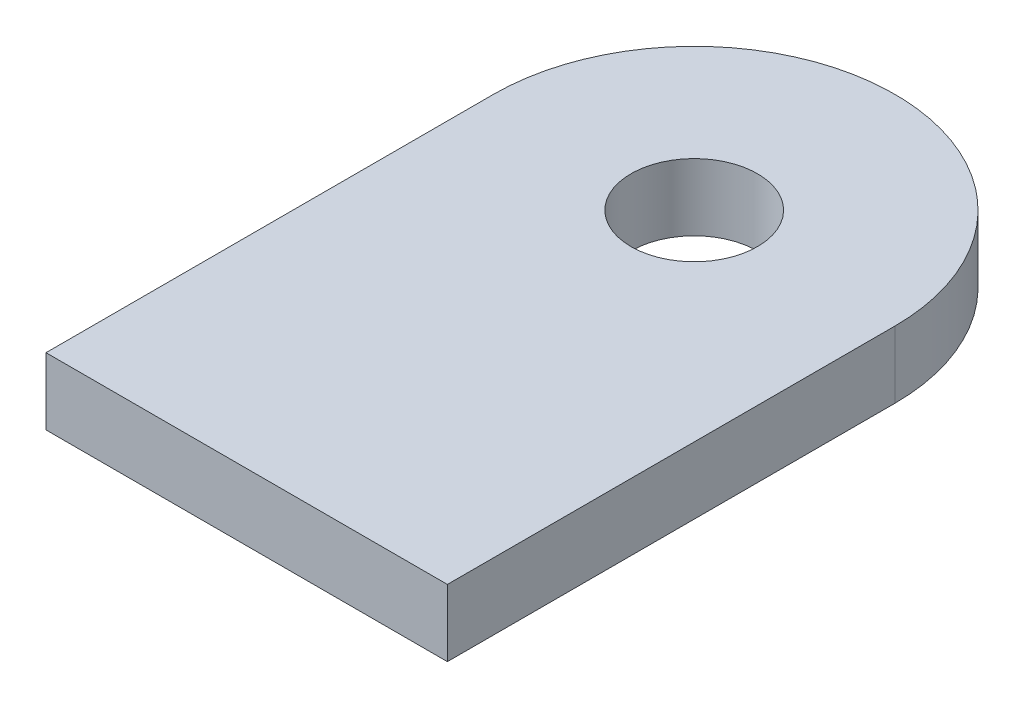
SolidWorks part; units mm, degrees
material "AISI 4340 Steel, annealed"
ref_plane "X-Y Datum" through (0, 0, 0) normal (0, 0, 1) x (1, 0, 0)
ref_plane "X-Z Datum" through (0, 0, 0) normal (0, 1, 0) x (1, 0, 0)
ref_plane "Y-Z Datum" through (0, 0, 0) normal (1, 0, 0) x (0, 0, -1)
sketch "Sketch1" plane through (0, 0, 0) normal (0, 1, 0) x (1, 0, 0)
  line L0 (-9.525, 0) -> (-9.525, -21.24)
  line L1 (9.525, 0) -> (9.525, -21.24)
  line L2 (-9.525, -21.24) -> (9.525, -21.24)
  line L3 (0, 0) -> (0, 50000) construction
  line L4 (0, 0) -> (-50000, 0) construction
  circle A0 centre (0, 0) radius 3
  circle A1 centre (0, 0) radius 9.525 construction
  arc A2 (-9.525, 0) -> (9.525, 0) centre (0, 0) cw
  dimension "D1" = 6
  dimension "D3" = 19.05
  dimension "D2" = 21.24
extrude "Boss-Extrude1" add sketch "Sketch1" along normal blind 3.175
